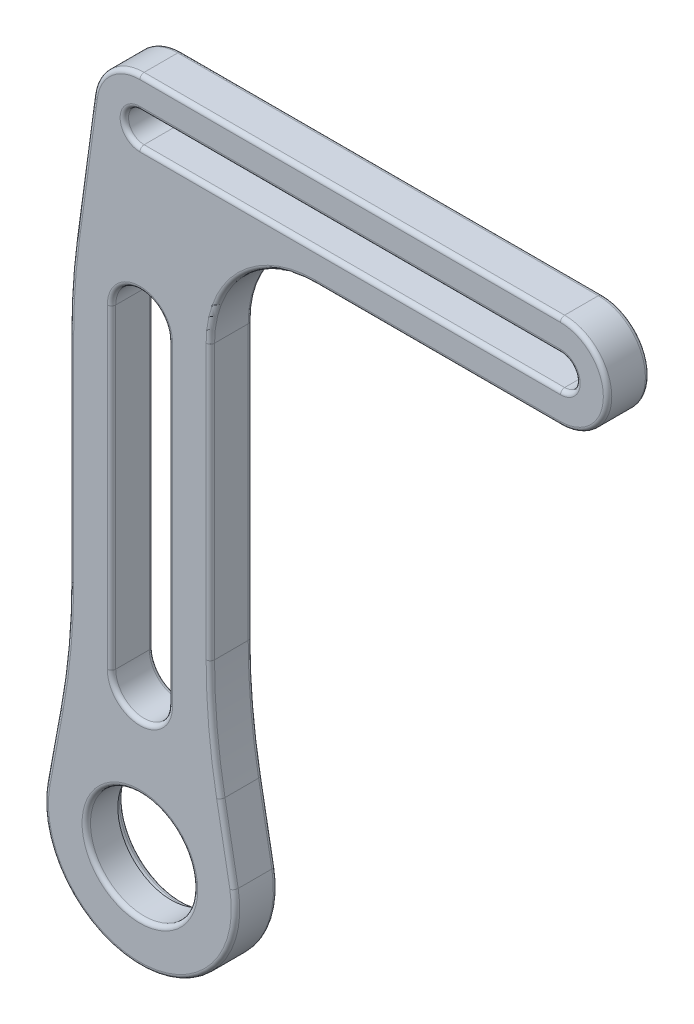
SolidWorks part; units mm, degrees
material "Polymaker PLA"
ref_plane "Front Plane" through (0, 0, 0) normal (0, 0, 1) x (1, 0, 0)
ref_plane "Top Plane" through (0, 0, 0) normal (0, 1, 0) x (1, 0, 0)
ref_plane "Right Plane" through (0, 0, 0) normal (1, 0, 0) x (0, 0, -1)
sketch "Sketch1" plane through (0, 0, 0) normal (0, 0, 1) x (1, 0, 0)
  line L0 (-10.795, -25.4) -> (-10.795, 50.687) construction
  line L1 (-10.795, -7.7734) -> (-10.795, 30.3266) construction
  line L2 (-14.224, -7.7734) -> (-14.224, 30.3266)
  line L3 (-7.366, -7.7734) -> (-7.366, 30.3266)
  line L4 (-19.304, -7.7734) -> (-19.304, 30.3266)
  line L5 (-2.286, -7.7734) -> (-2.286, 30.3266)
  line L6 (-19.304, -7.7734) -> (-22.1614, -23.3095)
  line L7 (-2.286, -7.7734) -> (0.5714, -23.3095)
  line L8 (-10.795, 50.687) -> (40.005, 50.687) construction
  line L9 (-10.795, 50.687) -> (40.005, 50.687) construction
  line L10 (-10.795, 52.5666) -> (40.005, 52.5666)
  line L11 (-10.795, 48.8074) -> (40.005, 48.8074)
  line L12 (-10.795, 56.3766) -> (40.005, 56.3766)
  line L13 (-2.286, 44.9974) -> (40.005, 44.9974)
  line L14 (-19.304, 30.3266) -> (-16.4328, 51.4532)
  line L15 (-2.286, 30.3266) -> (-2.286, 44.9974)
  line L16 (-10.795, 44.9974) -> (40.005, 44.9974) construction
  circle A0 centre (-10.795, -25.4) radius 14.605 construction
  circle A1 centre (-10.795, -25.4) radius 14.605 construction
  circle A2 centre (-10.795, -25.4) radius 6.35 construction
  circle A3 centre (-10.795, -25.4) radius 6.35 construction
  circle A4 centre (-10.795, -25.4) radius 6.477
  arc A5 (-14.224, -7.7734) -> (-7.366, -7.7734) centre (-10.795, -7.7734) ccw
  arc A6 (-7.366, 30.3266) -> (-14.224, 30.3266) centre (-10.795, 30.3266) ccw
  arc A9 (-19.304, -7.7734) -> (-2.286, -7.7734) centre (-10.795, -7.7734) ccw construction
  arc A10 (-22.1614, -23.3095) -> (0.5714, -23.3095) centre (-10.795, -25.4) ccw
  circle A11 centre (-10.795, -25.4) radius 11.557 construction
  arc A12 (-10.795, 52.5666) -> (-10.795, 48.8074) centre (-10.795, 50.687) ccw
  arc A13 (40.005, 48.8074) -> (40.005, 52.5666) centre (40.005, 50.687) ccw
  arc A14 (-2.286, 30.3266) -> (-19.304, 30.3266) centre (-10.795, 30.3266) ccw construction
  arc A15 (40.005, 44.9974) -> (40.005, 56.3766) centre (40.005, 50.687) ccw
  arc A16 (-10.795, 56.3766) -> (-16.4328, 51.4532) centre (-10.795, 50.687) ccw
  arc A17 (-10.795, 56.3766) -> (-10.795, 44.9974) centre (-10.795, 50.687) ccw construction
  point P9 (-10.795, 11.2766)
  point P12 (-10.795, 11.2766)
  point P30 (14.605, 50.687)
  dimension "D5" = 3.429
  dimension "D1" = 0.127
  dimension "D2" = 76.087
  dimension "D3" = 36.6766
  dimension "D4" = 19.05
  dimension "D6" = 5.08
  dimension "D8" = 3.7592
  dimension "D9" = 50.8
  dimension "D7" = 5.08
  dimension "D10" = 3.81
extrude "Boss-Extrude1" add sketch "Sketch1" along normal blind 3.81 and the other way blind 1.27
sketch "Sketch2" plane through (0, 0, 0) normal (0, 0, 1) x (1, 0, 0)
  circle A0 centre (-10.795, -25.4) radius 6.9469 construction
  circle A1 centre (-10.795, -25.4) radius 6.9469 construction
  circle A2 centre (-10.795, -25.4) radius 7.0739
  dimension "D1" = 0.127
extrude "Cut-Extrude1" cut sketch "Sketch2" against normal through all contours A2
fillet "Fillet2" radius 12.7 1 edges at (-2.286, 44.9974, 1.27)
fillet "Fillet3" radius 76.2 3 edges at (-19.304, 30.3266, 1.27) (-2.286, -7.7734, 1.27) (-19.304, -7.7734, 1.27)
fillet "Fillet1" radius 0.508 46 edges at (-19.304, 12.1739, 3.81) (-2.286, 15.7365, 3.81) (-0.2288, -18.9586, 3.81) (-10.795, -36.957, 3.81) (-21.3612, -18.9586, 3.81) (-14.224, 11.2766, 3.81) (-10.795, -11.2024, 3.81) (-7.366, 11.2766, 3.81) (-10.795, 33.7556, 3.81) (-4.318, -25.4, 3.81) (-10.795, -36.957, -1.27) (-0.2288, -18.9586, -1.27) (-2.286, 15.7365, -1.27) (-19.304, 12.1739, -1.27) (-21.3612, -18.9586, -1.27) (-7.366, 11.2766, -1.27) (-10.795, -11.2024, -1.27) (-14.224, 11.2766, -1.27) (-10.795, 33.7556, -1.27) (-3.7211, -25.4, -1.27) (45.6946, 50.687, 3.81) (25.2095, 44.9974, 3.81) (-17.5213, 43.4436, 3.81) (-14.5375, 54.9725, 3.81) (14.605, 56.3766, 3.81) (14.605, 52.5666, 3.81) (-12.6746, 50.687, 3.81) (14.605, 48.8074, 3.81) (41.8846, 50.687, 3.81) (-14.5375, 54.9725, -1.27) (-17.5213, 43.4436, -1.27) (25.2095, 44.9974, -1.27) (45.6946, 50.687, -1.27) (14.605, 56.3766, -1.27) (14.605, 48.8074, -1.27) (-12.6746, 50.687, -1.27) (14.605, 52.5666, -1.27) (41.8846, 50.687, -1.27) (1.4337, 41.2777, 3.81) (1.4337, 41.2777, -1.27) (-19.1303, 30.3149, 3.81) (-19.1303, 30.3149, -1.27) (-1.9711, -7.7447, 3.81) (-19.6189, -7.7447, 3.81) (-19.6189, -7.7447, -1.27) (-1.9711, -7.7447, -1.27)
ref_plane "SERVO_PIN_PLANE" through (-10.795, 0, 0) normal (-1, 0, 0) x (0, 0, 1)
ref_plane "MARKER_PIN_PLANE" through (0, 50.687, 0) normal (0, 1, 0) x (1, 0, 0)
equation "\"D2@Sketch1\"=\"ROCKER_ARM_LENGTH@SkeletonSketch-1.Part\""
equation "\"D3@Sketch1\"=\"SLOT_CENTER_DIST@SkeletonSketch-1.Part\""
equation "\"D4@Sketch1\"=\"SERVO_ARM_LENGTH@SkeletonSketch-1.Part\""
equation "\"D5@Sketch1\"=\"PIN_DIAMETER@ServoHorn-1.Part\"/2+.01"
